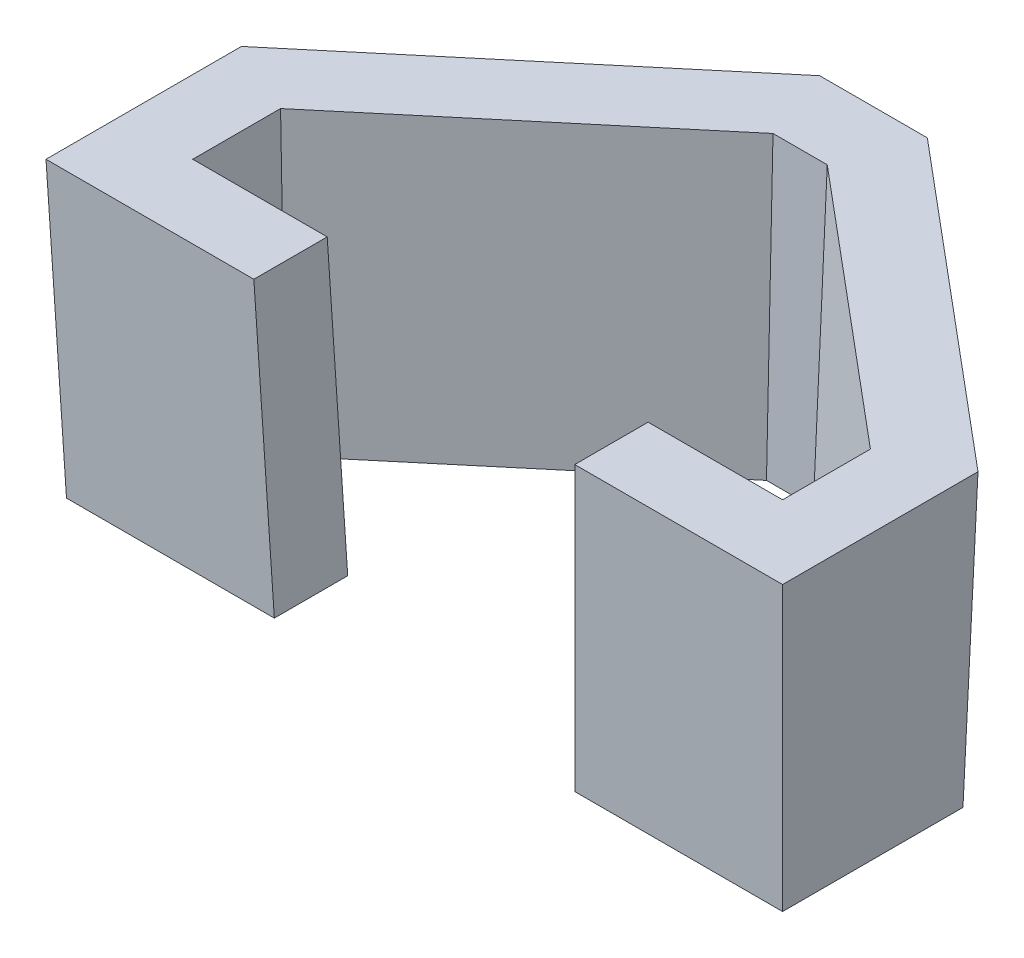
SolidWorks part; units mm, degrees
ref_plane "Alzado" through (0, 0, 0) normal (0, 0, 1) x (1, 0, 0)
ref_plane "Planta" through (0, 0, 0) normal (0, 1, 0) x (1, 0, 0)
ref_plane "Vista lateral" through (0, 0, 0) normal (1, 0, 0) x (0, 0, -1)
sketch "Croquis1" plane through (0, 0, 0) normal (0, 1, 0) x (1, 0, 0)
  line L0 (0, 0) -> (98.55, 0)
  line L1 (98.55, 0) -> (98.55, 12.6)
  line L2 (98.55, 12.6) -> (53.325, 50.5373)
  line L3 (53.325, 50.5373) -> (45.225, 50.5373)
  line L4 (45.225, 50.5373) -> (0, 12.6)
  line L5 (0, 12.6) -> (0, 0)
  point P7 (49.275, 50.5373)
  point P8 (49.275, 0)
  dimension "D1" = 98.55
  dimension "D2" = 8.1
  dimension "D3" = 59.03
  dimension "D4" = 59.03
  dimension "D5" = 12.6
extrude "Saliente-Extruir1" add sketch "Croquis1" along normal blind 8 draft 2 draft outward yes
sketch "Croquis10" plane through (0, 0, 0) normal (0, -1, 0) x (1, 0, 0)
  line L12 (-12.7, 12.7) -> (-12.7, -18.5232)
  line L13 (-12.7, -18.5232) -> (40.6036, -63.2373)
  line L14 (40.6036, -63.2373) -> (57.9464, -63.2373)
  line L15 (57.9464, -63.2373) -> (111.25, -18.5232)
  line L16 (111.25, -18.5232) -> (111.25, 12.7)
  line L17 (111.25, 12.7) -> (-12.7, 12.7)
  line L18 (-12.7, 12.7) -> (-12.7, -18.5232)
  line L19 (-12.7, -18.5232) -> (40.6036, -63.2373)
  line L20 (40.6036, -63.2373) -> (57.9464, -63.2373)
  line L21 (57.9464, -63.2373) -> (111.25, -18.5232)
  line L22 (111.25, -18.5232) -> (111.25, 12.7)
  line L23 (111.25, 12.7) -> (-12.7, 12.7)
  dimension "D1" = 12.7
extrude "Saliente-Extruir3" add sketch "Croquis10" against normal blind 75 draft 2 draft outward yes
sketch "Croquis11" plane through (0, 0, 0) normal (0, -1, 0) x (1, 0, 0)
  line L12 (98.55, 0) -> (0, 0)
  line L13 (98.55, -12.6) -> (98.55, 0)
  line L14 (53.325, -50.5373) -> (98.55, -12.6)
  line L15 (45.225, -50.5373) -> (53.325, -50.5373)
  line L16 (0, -12.6) -> (45.225, -50.5373)
  line L17 (0, 0) -> (0, -12.6)
  line L18 (98.55, 0) -> (0, 0)
  line L19 (98.55, -12.6) -> (98.55, 0)
  line L20 (53.325, -50.5373) -> (98.55, -12.6)
  line L21 (45.225, -50.5373) -> (53.325, -50.5373)
  line L22 (0, -12.6) -> (45.225, -50.5373)
  line L23 (0, 0) -> (0, -12.6)
  dimension "D1" = 0
extrude "Cortar-Extruir3" cut sketch "Croquis11" against normal through all draft 2 draft outward yes
sketch "Croquis13" plane through (0, 0, 0) normal (0, -1, 0) x (1, 0, 0)
  line L1 (0, 0) -> (0, -29.1767)
  line L3 (-12.7, -18.5232) -> (40.6036, -63.2373) construction
  line L4 (98.55, 0) -> (98.55, -29.1767)
  line L5 (57.9464, -63.2373) -> (111.25, -18.5232) construction
  line L18 (25.464, -50.5373) -> (73.086, -50.5373)
  line L19 (45.225, -50.5373) -> (53.325, -50.5373) construction
  line L20 (98.55, -12.6) -> (98.55, 0) construction
  line L21 (0, 0) -> (0, -12.6) construction
  line L22 (0, 0) -> (-12.7, 12.7)
  line L23 (98.55, 0) -> (111.25, 12.7)
sketch "Croquis14" plane through (0, 0, 0) normal (0, -1, 0) x (1, 0, 0)
  line L0 (111.25, 12.7) -> (-12.7, 12.7) construction
  line L1 (23.275, 0) -> (75.275, 0)
  line L2 (23.275, 0) -> (23.275, 12.7)
  line L3 (23.275, 12.7) -> (75.275, 12.7)
  line L4 (75.275, 0) -> (75.275, 12.7)
  line L5 (23.275, 0) -> (75.275, 12.7) construction
  line L6 (23.275, 12.7) -> (75.275, 0) construction
  line L7 (25.464, -50.5373) -> (73.086, -50.5373) construction
  line L8 (98.55, 0) -> (0, 0) construction
  point P0 (49.275, 6.35)
  point P7 (75.275, 6.35)
  point P11 (49.275, -50.5373)
  dimension "D1" = 52
extrude "Cortar-Extruir4" cut sketch "Croquis14" against normal through all draft 2 draft outward yes
sketch "Croquis16" plane through (0, 75, 0) normal (0, 1, 0) x (1, 0, 0)
  line L48 (101.1691, -2.6191) -> (77.8941, -2.6191)
  line L49 (77.8941, -2.6191) -> (77.8941, -15.3191)
  line L50 (77.8941, -15.3191) -> (113.8691, -15.3191)
  line L51 (113.8691, -15.3191) -> (113.8691, 19.7447)
  line L52 (113.8691, 19.7447) -> (58.8994, 65.8564)
  line L53 (58.8994, 65.8564) -> (39.6506, 65.8564)
  line L54 (39.6506, 65.8564) -> (-15.3191, 19.7447)
  line L55 (-15.3191, 19.7447) -> (-15.3191, -15.3191)
  line L56 (-15.3191, -15.3191) -> (20.6559, -15.3191)
  line L57 (20.6559, -15.3191) -> (20.6559, -2.6191)
  line L58 (20.6559, -2.6191) -> (-2.6191, -2.6191)
  line L59 (-2.6191, -2.6191) -> (-2.6191, 13.8215)
  line L60 (-2.6191, 13.8215) -> (44.272, 53.1564)
  line L61 (44.272, 53.1564) -> (54.278, 53.1564)
  line L62 (54.278, 53.1564) -> (101.1691, 13.8215)
  line L63 (101.1691, 13.8215) -> (101.1691, -2.6191)
  line L64 (101.1691, -2.6191) -> (77.8941, -2.6191)
  line L65 (77.8941, -2.6191) -> (77.8941, -15.3191)
  line L66 (77.8941, -15.3191) -> (113.8691, -15.3191)
  line L67 (113.8691, -15.3191) -> (113.8691, 19.7447)
  line L68 (113.8691, 19.7447) -> (58.8994, 65.8564)
  line L69 (58.8994, 65.8564) -> (39.6506, 65.8564)
  line L70 (39.6506, 65.8564) -> (-15.3191, 19.7447)
  line L71 (-15.3191, 19.7447) -> (-15.3191, -15.3191)
  line L72 (-15.3191, -15.3191) -> (20.6559, -15.3191)
  line L73 (20.6559, -15.3191) -> (20.6559, -2.6191)
  line L74 (20.6559, -2.6191) -> (-2.6191, -2.6191)
  line L75 (-2.6191, -2.6191) -> (-2.6191, 13.8215)
  line L76 (-2.6191, 13.8215) -> (44.272, 53.1564)
  line L77 (44.272, 53.1564) -> (54.278, 53.1564)
  line L78 (54.278, 53.1564) -> (101.1691, 13.8215)
  line L79 (101.1691, 13.8215) -> (101.1691, -2.6191)
  dimension "D1" = 0
extrude "Cortar-Extruir5" cut sketch "Croquis16" against normal blind 24.2 draft 2 draft outward yes
sketch "Croquis17" plane through (0, -0.443, 12.6845) normal (0, -0.0349, 0.9994) x (1, 0, 0)
  line L4 (113.024, 51.2742) -> (77.049, 51.2742)
  line L5 (77.049, 51.2742) -> (75.275, 0.4432)
  line L6 (75.275, 0.4432) -> (111.25, 0.4432)
  line L7 (111.25, 0.4432) -> (113.024, 51.2742)
  line L9 (77.049, 51.2742) -> (75.275, 0.4432)
  line L10 (75.275, 0.4432) -> (111.25, 0.4432)
  line L11 (111.25, 0.4432) -> (113.024, 51.2742)
  line L13 (113.024, 51.2742) -> (77.049, 51.2742)
  point P2 (0, 0)
  point P4 (0, 0)
  dimension "D1" = 0
